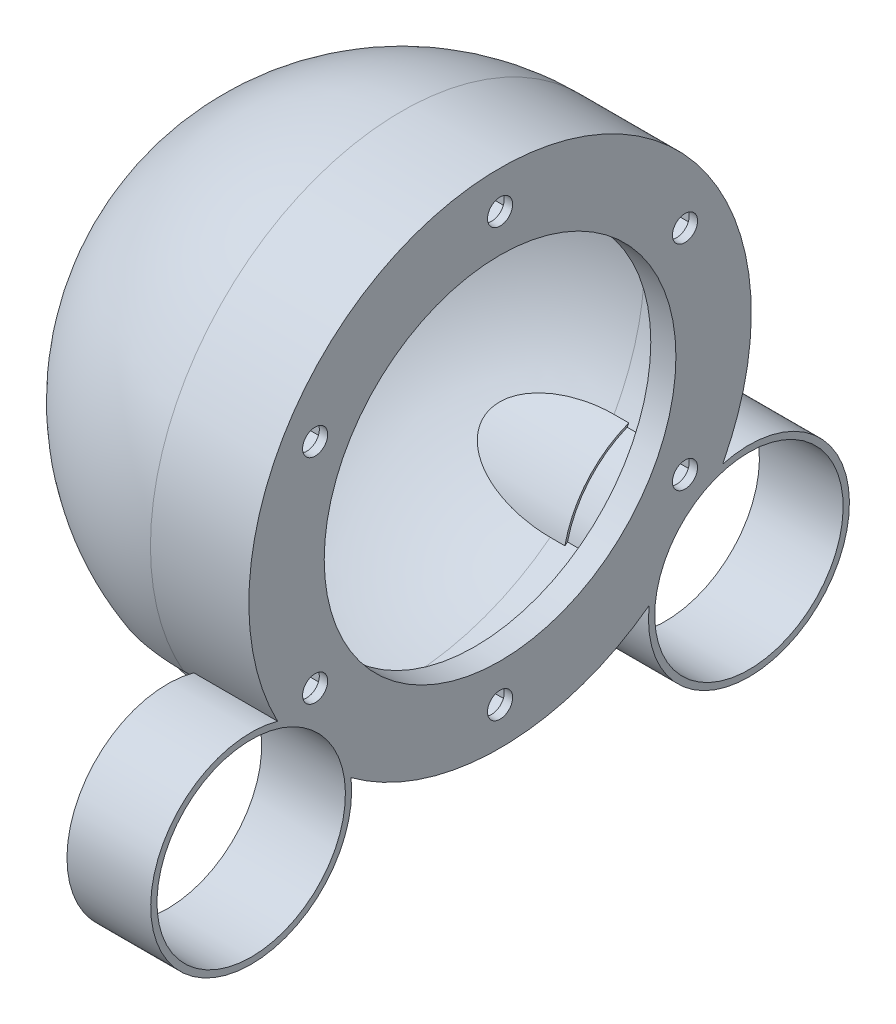
SolidWorks part; units mm, degrees
material "PVC Rígido"
ref_plane "Alzado" through (0, 0, 0) normal (0, 0, 1) x (1, 0, 0)
ref_plane "Planta" through (0, 0, 0) normal (0, 1, 0) x (1, 0, 0)
ref_plane "Vista lateral" through (0, 0, 0) normal (1, 0, 0) x (0, 0, -1)
sketch "Croquis4" plane through (0, 0, 0) normal (1, 0, 0) x (0, 0, -1)
  line L0 (-60, 0) -> (60, 0) construction
  line L1 (-60, 0) -> (60, 0)
  arc A0 (60, 0) -> (-60, 0) centre (0, 0) ccw
  dimension "D1" = 60
revolve "Revolución3" add sketch "Croquis4" angle 180 about L0
shell "Vaciado1" thickness 2
sketch "Croquis5" plane through (0, 0, 0) normal (1, 0, 0) x (0, 0, -1)
  circle A0 centre (0, 0) radius 60
  circle A1 centre (0, 0) radius 58
  dimension "D1" = 120
  dimension "D2" = 2
extrude "Saliente-Extruir1" add sketch "Croquis5" along normal blind 17.5
sketch "Croquis6" plane through (17.5, 0, 0) normal (1, 0, 0) x (0, 0, -1)
  line L0 (0, 0) -> (0, 60) construction
  circle A0 centre (0, 0) radius 60
  circle A1 centre (0, 0) radius 42
  circle A2 centre (0, 51) radius 3
  circle A3 centre (44.1673, 25.5) radius 3
  circle A4 centre (44.1673, -25.5) radius 3
  circle A5 centre (0, -51) radius 3
  circle A6 centre (-44.1673, -25.5) radius 3
  circle A7 centre (-44.1673, 25.5) radius 3
  point P20 (0, 0)
  dimension "D1" = 120
  dimension "D2" = 18
  dimension "D3" = 51
  dimension "D4" = 6
  dimension "D5" = 6
extrude "Saliente-Extruir2" add sketch "Croquis6" along normal blind 6
sketch "Croquis7" plane through (23.5, 0, 0) normal (1, 0, 0) x (0, 0, -1)
  line L0 (0, 0) -> (0, -29.9675) construction
  circle A0 centre (59.4392, -51) radius 24
  circle A4 centre (59.4392, -51) radius 22.5
  circle A5 centre (-59.4392, -51) radius 22.5
  circle A6 centre (-59.4392, -51) radius 24
  point P8 (0, -51)
  dimension "D2" = 48
  dimension "D3" = 45
  dimension "D1" = 78.32
extrude "Saliente-Extruir3" add sketch "Croquis7" against normal blind 20
sketch "Croquis8" plane through (23.5, 0, 0) normal (1, 0, 0) x (0, 0, -1)
  line L0 (0, 0) -> (0, -20.2497) construction
  circle A0 centre (-59.4392, -51) radius 22.5
  circle A1 centre (59.4392, -51) radius 22.5
  dimension "D1" = 45
extrude "Cortar-Extruir2" cut sketch "Croquis8" against normal blind 20
ref_plane "Plano1" through (3.5, 0, 0) normal (1, 0, 0) x (0, 0, -1)
sketch "Croquis9" plane through (3.5, 0, 0) normal (1, 0, 0) x (0, 0, -1)
  line L0 (0, 0) -> (0, -18.8301) construction
  circle A0 centre (-59.4392, -51) radius 22.5
  circle A1 centre (59.4392, -51) radius 22.5
  dimension "D1" = 45
extrude "Cortar-Extruir3" cut sketch "Croquis9" against normal through all
sketch "Croquis10" plane through (3.5, 0, 0) normal (1, 0, 0) x (0, 0, -1)
  line L0 (0, 0) -> (0, -12.2722) construction
  arc A0 (-37.2979, -46.9986) -> (-52.1201, -29.7237) centre (-59.4392, -51) ccw
  arc A1 (-35.0474, -48.6999) -> (-53.4596, -27.2409) centre (-59.4392, -51) ccw
  arc A2 (-37.2979, -46.9986) -> (-35.0474, -48.6999) centre (0, 0) ccw
  arc A3 (-53.4596, -27.2409) -> (-52.1201, -29.7237) centre (0, 0) ccw
  arc A4 (37.2979, -46.9986) -> (35.0474, -48.6999) centre (0, 0) cw
  arc A5 (53.4596, -27.2409) -> (52.1201, -29.7237) centre (0, 0) cw
  arc A6 (35.0474, -48.6999) -> (53.4596, -27.2409) centre (59.4392, -51) cw
  arc A7 (37.2979, -46.9986) -> (52.1201, -29.7237) centre (59.4392, -51) cw
  dimension "D1" = 45
  dimension "D2" = 49
  dimension "D3" = 120
extrude "Saliente-Extruir4" add sketch "Croquis10" against normal up to body
sketch "Croquis11" plane through (17.5, 0, 0) normal (-1, 0, 0) x (0, 0, 1)
  line L0 (48.1673, 27.8094) -> (44.1673, 30.1188)
  line L1 (0, 55.6188) -> (-4, 53.3094)
  line L2 (-4, 53.3094) -> (-4, 48.6906)
  line L3 (-4, 48.6906) -> (0, 46.3812)
  line L4 (0, 46.3812) -> (4, 48.6906)
  line L5 (4, 48.6906) -> (4, 53.3094)
  line L6 (4, 53.3094) -> (0, 55.6188)
  line L7 (44.1673, 30.1188) -> (40.1673, 27.8094)
  line L8 (40.1673, 27.8094) -> (40.1673, 23.1906)
  line L9 (40.1673, 23.1906) -> (44.1673, 20.8812)
  line L10 (44.1673, 20.8812) -> (48.1673, 23.1906)
  line L11 (48.1673, 23.1906) -> (48.1673, 27.8094)
  line L12 (48.1673, -27.8094) -> (48.1673, -23.1906)
  line L13 (48.1673, -23.1906) -> (44.1673, -20.8812)
  line L14 (44.1673, -20.8812) -> (40.1673, -23.1906)
  line L15 (40.1673, -23.1906) -> (40.1673, -27.8094)
  line L16 (40.1673, -27.8094) -> (44.1673, -30.1188)
  line L17 (44.1673, -30.1188) -> (48.1673, -27.8094)
  line L18 (0, -55.6188) -> (4, -53.3094)
  line L19 (4, -53.3094) -> (4, -48.6906)
  line L20 (4, -48.6906) -> (0, -46.3812)
  line L21 (0, -46.3812) -> (-4, -48.6906)
  line L22 (-4, -48.6906) -> (-4, -53.3094)
  line L23 (-4, -53.3094) -> (0, -55.6188)
  line L24 (-48.1673, -27.8094) -> (-44.1673, -30.1188)
  line L25 (-44.1673, -30.1188) -> (-40.1673, -27.8094)
  line L26 (-40.1673, -27.8094) -> (-40.1673, -23.1906)
  line L27 (-40.1673, -23.1906) -> (-44.1673, -20.8812)
  line L28 (-44.1673, -20.8812) -> (-48.1673, -23.1906)
  line L29 (-48.1673, -23.1906) -> (-48.1673, -27.8094)
  line L30 (-48.1673, 27.8094) -> (-48.1673, 23.1906)
  line L31 (-48.1673, 23.1906) -> (-44.1673, 20.8812)
  line L32 (-44.1673, 20.8812) -> (-40.1673, 23.1906)
  line L33 (-40.1673, 23.1906) -> (-40.1673, 27.8094)
  line L34 (-40.1673, 27.8094) -> (-44.1673, 30.1188)
  line L35 (-44.1673, 30.1188) -> (-48.1673, 27.8094)
  circle A0 centre (0, 51) radius 4 construction
  point P42 (0, 0)
  dimension "D1" = 8
  dimension "D2" = 6
extrude "Cortar-Extruir4" cut sketch "Croquis11" against normal blind 4
